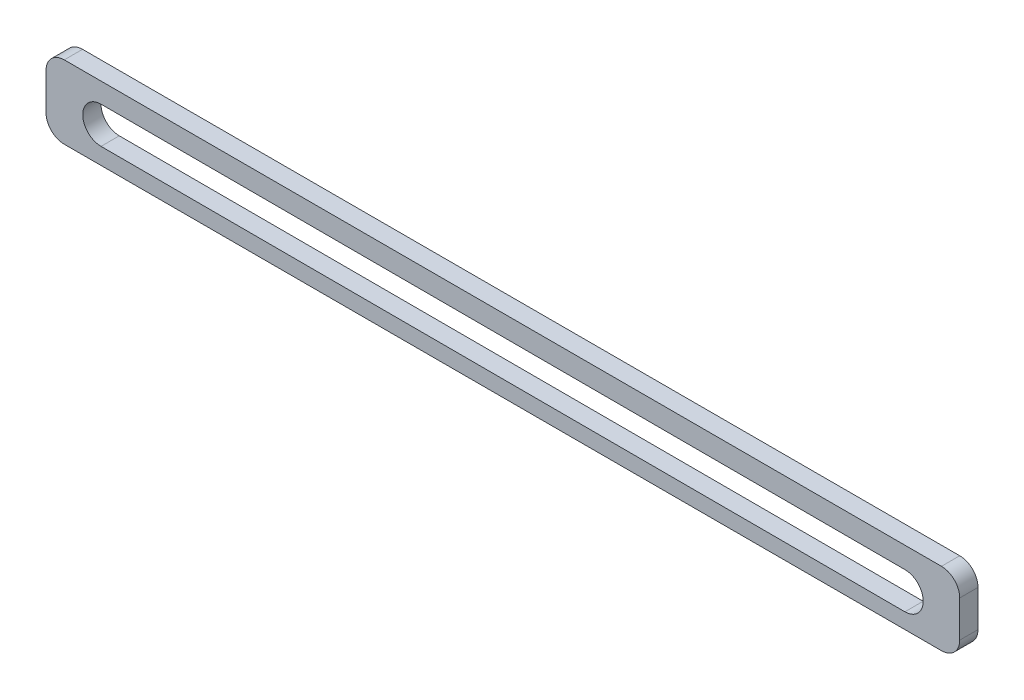
SolidWorks part; units mm, degrees
ref_plane "Front Plane" through (0, 0, 0) normal (0, 0, 1) x (1, 0, 0)
ref_plane "Top Plane" through (0, 0, 0) normal (0, 1, 0) x (1, 0, 0)
ref_plane "Right Plane" through (0, 0, 0) normal (1, 0, 0) x (0, 0, -1)
sketch "Sketch1" plane through (0, 0, 0) normal (0, 0, 1) x (1, 0, 0)
  line L0 (-200, 153.2621) -> (-170, 153.2621) construction
  line L1 (-169.8814, 132.3226) -> (270.0184, 131.7022) construction
  line L2 (-190, 153.2621) -> (290, 153.2621)
  line L3 (-200, 143.2621) -> (-200, 123.2621)
  line L4 (-190, 113.2621) -> (290, 113.2621)
  line L5 (300, 143.2621) -> (300, 123.2621)
  line L6 (-200, 153.2621) -> (300, 113.2621) construction
  line L7 (-200, 113.2621) -> (300, 153.2621) construction
  line L8 (300, 153.2621) -> (270, 153.2621) construction
  line L9 (-170, 153.2621) -> (-170, 113.2621) construction
  line L10 (270, 153.2621) -> (270, 113.2621) construction
  line L11 (-169.8673, 142.3226) -> (270.0325, 141.7022)
  line L12 (-169.8955, 122.3226) -> (270.0043, 121.7022)
  arc A0 (290, 113.2621) -> (300, 123.2621) centre (290, 123.2621) ccw
  arc A1 (290, 153.2621) -> (300, 143.2621) centre (290, 143.2621) cw
  arc A2 (-200, 123.2621) -> (-190, 113.2621) centre (-190, 123.2621) ccw
  arc A3 (-190, 153.2621) -> (-200, 143.2621) centre (-190, 143.2621) ccw
  arc A6 (-169.8673, 142.3226) -> (-169.8955, 122.3226) centre (-169.8814, 132.3226) ccw
  arc A7 (270.0043, 121.7022) -> (270.0325, 141.7022) centre (270.0184, 131.7022) ccw
  point P0 (50, 133.2621)
  point P1 (50.0685, 132.0124)
  dimension "D3" = 10
  dimension "D1" = 500
  dimension "D2" = 40
extrude "Boss-Extrude1" add sketch "Sketch1" along normal mid plane 10
